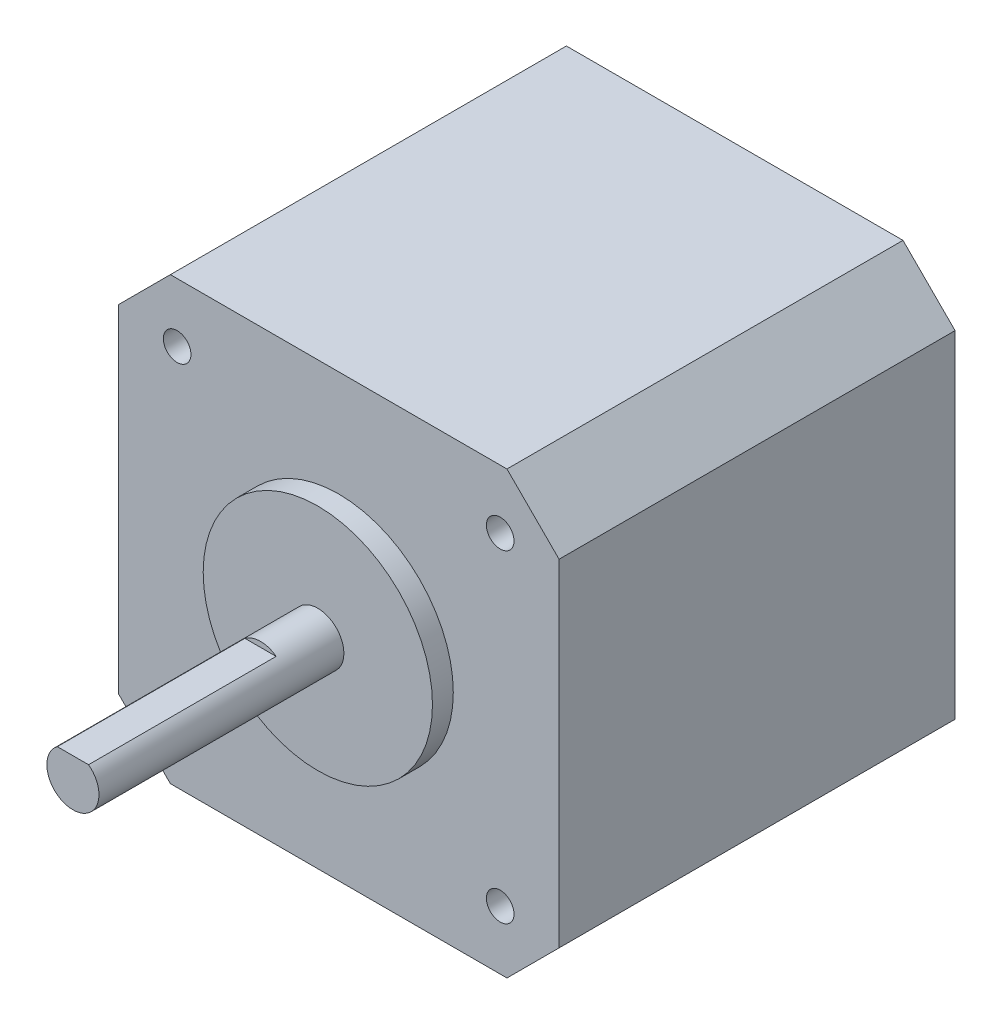
SolidWorks part; units mm, degrees
material "AISI 1020"
ref_plane "Спереди" through (0, 0, 0) normal (0, 0, 1) x (1, 0, 0)
ref_plane "Сверху" through (0, 0, 0) normal (0, 1, 0) x (1, 0, 0)
ref_plane "Справа" through (0, 0, 0) normal (1, 0, 0) x (0, 0, -1)
sketch "Эскиз1" plane through (0, 0, 0) normal (0, 0, 1) x (1, 0, 0)
  line L0 (-21.15, 16.15) -> (-16.15, 21.15)
  line L1 (-16.15, -21.15) -> (16.15, -21.15)
  line L2 (-21.15, -16.15) -> (-21.15, 16.15)
  line L3 (-16.15, 21.15) -> (16.15, 21.15)
  line L4 (21.15, -16.15) -> (21.15, 16.15)
  line L5 (-21.15, -21.15) -> (21.15, 21.15) construction
  line L6 (-21.15, 21.15) -> (21.15, -21.15) construction
  line L7 (16.15, 21.15) -> (21.15, 16.15)
  line L8 (16.15, -21.15) -> (21.15, -16.15)
  line L9 (-21.15, -16.15) -> (-16.15, -21.15)
  point P0 (0, 0)
  dimension "D1" = 42.3
extrude "Бобышка-Вытянуть1" add sketch "Эскиз1" against normal blind 38
sketch "Эскиз2" plane through (0, 0, 0) normal (0, 0, 1) x (1, 0, 0)
  line L1 (-15.5, -15.5) -> (15.5, -15.5)
  line L2 (-15.5, -15.5) -> (-15.5, 15.5)
  line L3 (-15.5, 15.5) -> (15.5, 15.5)
  line L4 (15.5, -15.5) -> (15.5, 15.5)
  line L5 (-15.5, -15.5) -> (15.5, 15.5) construction
  line L6 (-15.5, 15.5) -> (15.5, -15.5) construction
  point P0 (0, 0)
  dimension "D1" = 31
hole_wizard "Отверстие обработанное метчиком M3x0.351" positions "Эскиз5" profile "Эскиз4" tap size "M3x0.35" standard "DIN"
sketch "Эскиз5" plane through (0, 0, 0) normal (0, 0, 1) x (1, 0, 0)
  point P0 (-15.5, 15.5)
  point P3 (15.5, 15.5)
  point P6 (15.5, -15.5)
  point P9 (-15.5, -15.5)
sketch "Эскиз4" plane through (-15.5, 15.5, 0) normal (1, 0, 0) x (0, -1, 0)
  line L0 (0, 0) -> (0, 8.5461)
  line L1 (0, 8.5461) -> (1.325, 7.75)
  line L2 (1.325, 7.75) -> (1.325, 0)
  line L5 (1.325, 0) -> (0, 0)
  line L10 (0, 8.5461) -> (-1.325, 7.75) construction
  line L11 (0, -6.35) -> (0, 107.95) construction
  dimension "Диаметр сверла" = 2.65
  dimension "Глубина сверла" = 7.75
  dimension "Угол заточки сверла" = 118
cosmetic thread "Отверстие резьбы1" parameters "D1"=6, "D2"=3
cosmetic thread "Отверстие резьбы2" parameters "D1"=6, "D2"=3
cosmetic thread "Отверстие резьбы3" parameters "D1"=6, "D2"=3
cosmetic thread "Отверстие резьбы4" parameters "D1"=6, "D2"=3
sketch "Эскиз6" plane through (0, 0, 0) normal (0, 0, 1) x (1, 0, 0)
  circle A0 centre (0, 0) radius 11
  dimension "D1" = 22
extrude "Бобышка-Вытянуть2" add sketch "Эскиз6" along normal blind 2
sketch "Эскиз7" plane through (0, 0, 2) normal (0, 0, 1) x (1, 0, 0)
  circle A0 centre (0, 0) radius 2.5
  dimension "D1" = 5
extrude "Бобышка-Вытянуть3" add sketch "Эскиз7" along normal blind 23.5
sketch "Эскиз8" plane through (0, 0, 25.5) normal (0, 0, 1) x (1, 0, 0)
  line L0 (-1.5, 2) -> (1.5, 2)
  circle A0 centre (0, 0) radius 2.5 construction
  circle A1 centre (0, 0) radius 2.5 construction
  arc A2 (-1.5, 2) -> (1.5, 2) centre (0, 0) cw
  dimension "D1" = 4.5
extrude "Вырез-Вытянуть1" cut sketch "Эскиз8" against normal blind 18
